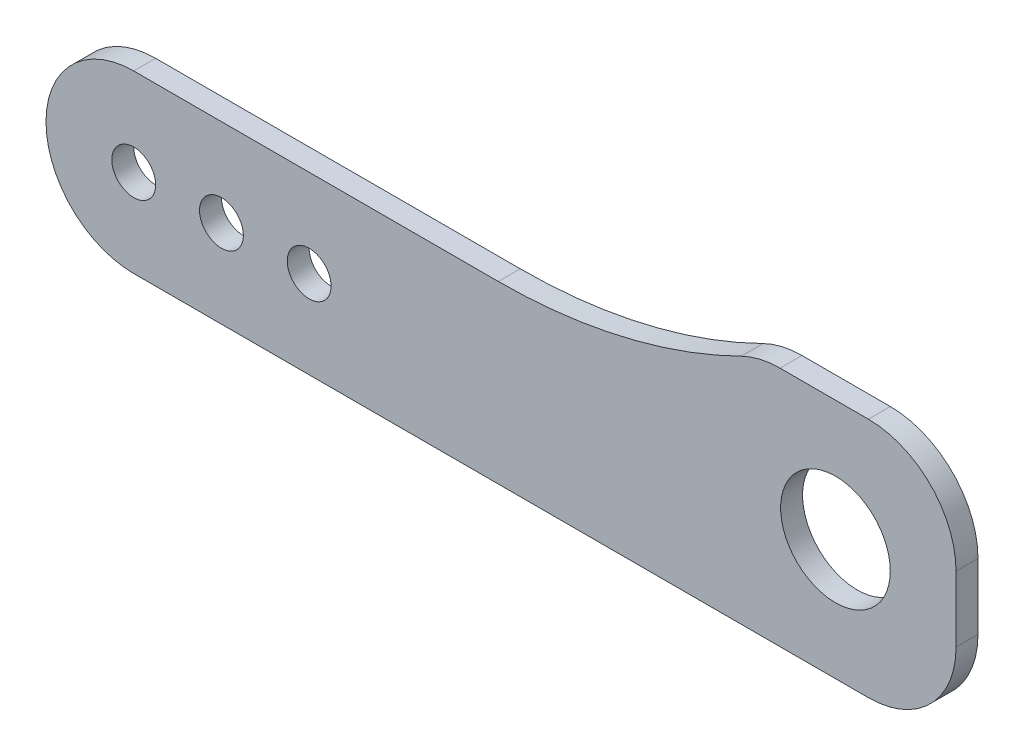
SolidWorks part; units mm, degrees
ref_plane "Front Plane" through (0, 0, 0) normal (0, 0, 1) x (1, 0, 0)
ref_plane "Top Plane" through (0, 0, 0) normal (0, 1, 0) x (1, 0, 0)
ref_plane "Right Plane" through (0, 0, 0) normal (1, 0, 0) x (0, 0, -1)
sketch "Sketch1" plane through (0, 0, 0) normal (0, 0, 1) x (1, 0, 0)
  line L0 (0, 8) -> (33.2513, 8)
  line L1 (67, -8) -> (0, -8)
  line L5 (58.9418, 14) -> (67, 14)
  line L6 (75, 0) -> (75, 6)
  arc A1 (0, -8) -> (0, 8) centre (0, 0) cw
  arc A2 (33.2513, 8) -> (55.3983, 13.1724) centre (33.2513, 58) ccw
  arc A3 (67, -8) -> (75, 0) centre (67, 0) ccw
  arc A4 (67, 14) -> (75, 6) centre (67, 6) cw
  arc A5 (58.9418, 14) -> (55.3983, 13.1724) centre (58.9418, 6) ccw
  point P3 (75, -8)
  point P15 (75, 14)
  point P18 (57, 14)
  dimension "D2" = 8
  dimension "D4" = 50
  dimension "D1" = 8
  dimension "D3" = 22
  dimension "D5" = 18
  dimension "D6" = 75
extrude "Boss-Extrude1" add sketch "Sketch1" along normal blind 2
sketch "Sketch2" plane through (0, 0, 2) normal (0, 0, 1) x (1, 0, 0)
  line L0 (-8, 0) -> (-8, -8) construction
  line L6 (0, 0) -> (8, 0) construction
  line L7 (8, 0) -> (16, 0) construction
  line L8 (-8, -8) -> (0, -8) construction
  circle A0 centre (0, 0) radius 2
  circle A2 centre (8, 0) radius 2
  circle A5 centre (16, 0) radius 2
  arc A6 (0, 8) -> (0, -8) centre (0, 0) ccw construction
  point P3 (14.3617, 2.9082)
  dimension "D1" = 4
  dimension "D2" = 8
extrude "Cut-Extrude1" cut sketch "Sketch2" against normal up to surface (2 mm away) up to face at (47.4617, 5.1223, 0)
sketch "Sketch3" plane through (0, 0, 2) normal (0, 0, 1) x (1, 0, 0)
  line L0 (75, 0) -> (75, 6) construction
  line L2 (64, 3) -> (75, 3) construction
  line L3 (64, 3) -> (64, -8) construction
  line L4 (0, -8) -> (67, -8) construction
  circle A0 centre (64, 3) radius 5
  dimension "D1" = 10
extrude "Cut-Extrude2" cut sketch "Sketch3" against normal up to surface (2 mm away) up to face at (2, 0, 0)
